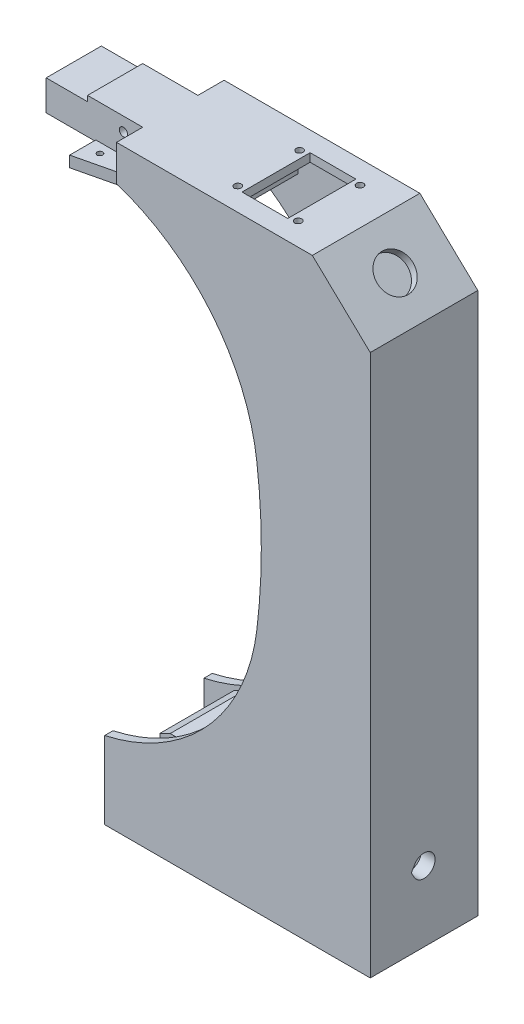
SolidWorks part; units mm, degrees
ref_plane "Спереди" through (0, 0, 0) normal (0, 0, 1) x (1, 0, 0)
ref_plane "Сверху" through (0, 0, 0) normal (0, 1, 0) x (1, 0, 0)
ref_plane "Справа" through (0, 0, 0) normal (1, 0, 0) x (0, 0, -1)
other "Configuration Table"
sketch "Эскиз1" plane through (0, 0, 0) normal (0, 0, 1) x (1, 0, 0)
  line L1 (4.2996, 175.4028) -> (4.2996, 188.4028)
  line L4 (96.2996, 0) -> (96.2996, 168.4028)
  line L7 (75.2996, 188.4028) -> (4.2996, 188.4028)
  line L11 (0, 0) -> (0, -28)
  line L12 (96.2996, 0) -> (96.2996, -28)
  line L13 (96.2996, -28) -> (0, -28)
  line L14 (75.2996, 188.4028) -> (96.2996, 168.4028)
  arc A0 (0, 0) -> (55.1731, 60.6624) centre (-15.2954, 69.3329) ccw
  arc A1 (55.1731, 113.6624) -> (4.2996, 175.4028) centre (-18.7693, 104.5645) ccw
  arc A2 (55.1731, 60.6624) -> (55.1731, 113.6624) centre (-160.2027, 87.1624) ccw
  dimension "D1" = 142
  dimension "D3" = 149
  dimension "D5" = 53
  dimension "D6" = 217
  dimension "D2" = 82
  dimension "D4" = 80
  dimension "D7" = 125.5129
  dimension "D8" = 126.3456
  dimension "D9" = 15.2954
  dimension "D10" = 69.3329
  dimension "D11" = 160.2027
  dimension "D12" = 87.1624
  dimension "D13" = 104.5645
  dimension "D14" = 18.7693
  dimension "D15" = 4.2996
  dimension "D16" = 175.4028
  dimension "D17" = 92
  dimension "D18" = 168.4028
  dimension "D19" = 71
  dimension "D20" = 28
  dimension "D21" = 96.2996
  dimension "D22" = 28
  dimension "D23" = 20
  dimension "D24" = 216.4028
extrude "Бобышка-Вытянуть6" add sketch "Эскиз1" along normal blind 39
sketch "Эскиз5" plane through (0, 0, 0) normal (0, 0, 1) x (1, 0, 0)
  line L3 (34.0996, 175.4028) -> (4.2996, 175.4028)
  line L4 (-18.7004, 169.0219) -> (-18.7004, -25)
  line L8 (34.0996, 175.4028) -> (34.0996, 185.4028)
  line L9 (34.0996, 185.4028) -> (74.0996, 185.4028)
  line L10 (74.0996, 185.4028) -> (91.2996, 169.0219)
  line L11 (96.2996, 168.4028) -> (75.2996, 188.4028) construction
  line L12 (75.2996, 188.4028) -> (4.2996, 188.4028) construction
  line L13 (-18.7004, 169.0219) -> (4.2996, 169.0219)
  line L14 (4.2996, 169.0219) -> (4.2996, 175.4028)
  line L18 (0, -28) -> (96.2996, -28) construction
  line L20 (-18.7004, -25) -> (14, -25)
  line L21 (14, 6.5) -> (14, -25)
  line L22 (91.2996, -25) -> (30.2996, -25)
  line L25 (30.2996, -25) -> (30.2996, 6.5)
  line L27 (14, 6.5) -> (30.2996, 6.5)
  line L28 (91.2996, -25) -> (91.2996, 169.0219)
  line L29 (96.2996, -28) -> (96.2996, 168.4028) construction
  dimension "D2" = 32.7004
  dimension "D3" = 31.5
  dimension "D4" = 3
  dimension "D5" = 3
  dimension "D6" = 40
  dimension "D7" = 23
  dimension "D8" = 5
  dimension "D9" = 6.381
  dimension "D10" = 14
  dimension "D11" = 3
  dimension "D12" = 3
  dimension "D14" = 61
extrude "Вырез-Вытянуть2" cut sketch "Эскиз5" along normal blind 33 from offset 3
sketch "Эскиз7" plane through (0, 0, 0) normal (0, 0, 1) x (1, 0, 0)
  line L1 (4.2996, 188.4028) -> (-30.7004, 188.4028)
  line L2 (4.2996, 188.4028) -> (4.2996, 175.4028)
  line L3 (4.2996, 175.4028) -> (-30.7004, 175.4028)
  line L4 (-30.7004, 188.4028) -> (-30.7004, 175.4028)
  dimension "D1" = 35
extrude "Бобышка-Вытянуть7" add sketch "Эскиз7" along normal blind 20 from offset 9.5
sketch "Эскиз22" plane through (0, 188.4028, 0) normal (0, 1, 0) x (1, 0, 0)
  line L0 (10.2996, -29.5) -> (10.2996, -33.5375)
  line L1 (4.2996, -9.5) -> (-30.7004, -9.5) construction
  line L2 (-12.7004, -9.5) -> (-12.7004, 0)
  line L3 (-48.7653, 0) -> (48.7653, 0) construction
  line L4 (-12.7004, 0) -> (10.2996, -5.4625)
  line L5 (10.2996, -9.5) -> (-12.7004, -9.5)
  line L6 (4.2996, -29.5) -> (-30.7004, -29.5) construction
  line L7 (-12.7004, -29.5) -> (-12.7004, -39)
  line L8 (-12.7004, -39) -> (10.2996, -33.5375)
  line L9 (10.2996, -29.5) -> (-12.7004, -29.5)
  line L10 (10.2996, -9.5) -> (10.2996, -5.4625)
  dimension "D1" = 9.5
  dimension "D2" = 13.36
  dimension "D3" = 17
  dimension "D4" = 9.5
  dimension "D5" = 13.36
  dimension "D6" = 17
  dimension "D7" = 23
extrude "Бобышка-Вытянуть8" add sketch "Эскиз22" along normal blind 4 from offset 16.5 offset against normal yes
sketch "Эскиз12" plane through (0, 0, 0) normal (0, 1, 0) x (1, 0, 0)
  line L1 (-7.7004, -34.1547) -> (-7.2004, -33.866)
  line L2 (-7.7004, -34.1547) -> (-8.2004, -33.866)
  line L4 (-7.7004, -7.1547) -> (-7.2004, -6.866)
  line L5 (-7.7004, -7.1547) -> (-8.2004, -6.866)
  arc A0 (-7.2004, -6.866) -> (-8.2004, -6.866) centre (-7.7004, -6) ccw
  arc A1 (-7.2004, -33.866) -> (-8.2004, -33.866) centre (-7.7004, -33) ccw
  dimension "D1" = 2
  dimension "D2" = 2
  dimension "D3" = 27
  dimension "D4" = 6
  dimension "D5" = 23
  dimension "D6" = 23
  dimension "D7" = 120
  dimension "D8" = 120
  dimension "D9" = 0.5
  dimension "D10" = 0.5
extrude "Вырез-Вытянуть3" cut sketch "Эскиз12" against normal blind 10 from offset 180
sketch "Эскиз13" plane through (0, 0, 0) normal (0, 0, 1) x (1, 0, 0)
  line L0 (4.2996, 188.4028) -> (-30.7004, 188.4028) construction
  line L1 (-30.7004, 188.4028) -> (-30.7004, 175.4028) construction
  circle A0 centre (-2.7004, 183.4028) radius 1.5
  dimension "D1" = 5
  dimension "D3" = 3
  dimension "D2" = 28
extrude "Вырез-Вытянуть4" cut sketch "Эскиз13" along normal blind 30
sketch "Эскиз14" plane through (0, 0, 0) normal (0, 0, 1) x (1, 0, 0)
  line L1 (-30.7004, 188.4028) -> (-15.7004, 188.4028)
  line L2 (-30.7004, 188.4028) -> (-30.7004, 186.4028)
  line L3 (-30.7004, 186.4028) -> (-15.7004, 186.4028)
  line L4 (-15.7004, 188.4028) -> (-15.7004, 186.4028)
  dimension "D1" = 2
  dimension "D2" = 15
extrude "Вырез-Вытянуть5" cut sketch "Эскиз14" along normal blind 30
sketch "Эскиз17" plane through (0, 0, 0) normal (1, 0, 0) x (0, 0, -1)
  line L1 (-24.1188, -2.5) -> (-22.9641, -0.5)
  line L2 (-24.1188, -2.5) -> (-22.9641, -4.5)
  arc A0 (-22.9641, -4.5) -> (-22.9641, -0.5) centre (-19.5, -2.5) ccw
  dimension "D1" = 8
  dimension "D2" = 2.5
  dimension "D3" = 19.5
  dimension "D4" = 120
  dimension "D5" = 2
extrude "Вырез-Вытянуть7" cut sketch "Эскиз17" along normal blind 85 from offset 17
sketch "Эскиз18" plane through (0, 0, 0) normal (1, 0, 0) x (0, 0, -1)
  line L1 (-21.8094, -2.5) -> (-21.2321, -1.5)
  line L2 (-21.8094, -2.5) -> (-21.2321, -3.5)
  arc A0 (-21.2321, -3.5) -> (-21.2321, -1.5) centre (-19.5, -2.5) ccw
  dimension "D1" = 4
  dimension "D2" = 120
  dimension "D3" = 1
extrude "Вырез-Вытянуть9" cut sketch "Эскиз18" along normal blind 5 from offset 13
sketch "Эскиз20" plane through (0, 188.4028, 0) normal (0, 1, 0) x (1, 0, 0)
  line L4 (42.65, -7.15) -> (42.65, -31.85)
  line L5 (42.65, -31.85) -> (59.25, -31.85)
  line L6 (42.65, -7.15) -> (59.25, -7.15)
  line L7 (59.25, -7.15) -> (59.25, -31.85)
  line L9 (40, -32.1434) -> (40.625, -31.7825)
  line L10 (40, -32.1434) -> (39.375, -31.7825)
  line L12 (40, -9.7434) -> (40.625, -9.3825)
  line L13 (40, -9.7434) -> (39.375, -9.3825)
  line L16 (61.9, -9.7434) -> (62.525, -9.3825)
  line L17 (61.9, -9.7434) -> (61.275, -9.3825)
  line L20 (61.9, -32.1434) -> (62.525, -31.7825)
  line L21 (61.9, -32.1434) -> (61.275, -31.7825)
  arc A0 (62.525, -9.3825) -> (61.275, -9.3825) centre (61.9, -8.3) ccw
  arc A1 (62.525, -31.7825) -> (61.275, -31.7825) centre (61.9, -30.7) ccw
  arc A2 (40.625, -9.3825) -> (39.375, -9.3825) centre (40, -8.3) ccw
  arc A3 (40.625, -31.7825) -> (39.375, -31.7825) centre (40, -30.7) ccw
  dimension "D1" = 21.9
  dimension "D13" = 2.5
  dimension "D14" = 2.5
  dimension "D15" = 2.5
  dimension "D16" = 2.5
  dimension "D2" = 22.4
  dimension "D3" = 16.6
  dimension "D4" = 24.7
  dimension "D5" = 40
  dimension "D6" = 21.9
  dimension "D7" = 22.4
  dimension "D8" = 31.3268
  dimension "D9" = 42.65
  dimension "D10" = 7.15
  dimension "D11" = 61.9
  dimension "D12" = 30.7
  dimension "D17" = 59.25
  dimension "D18" = 120
  dimension "D19" = 120
  dimension "D20" = 120
  dimension "D21" = 120
  dimension "D22" = 0.625
  dimension "D23" = 0.625
  dimension "D24" = 0.625
  dimension "D25" = 0.625
extrude "Вырез-Вытянуть10" cut sketch "Эскиз20" against normal blind 5
sketch "Эскиз21" plane through (129.9037, 136.3989, 0) normal (0.6897, 0.7241, 0) x (0, 0, -1)
  line L0 (0, 46.4057) -> (0, 75.4057) construction
  line L1 (0, 60.9057) -> (-39, 60.9057)
  line L2 (-39, 46.4057) -> (-39, 75.4057) construction
  line L3 (-19.5, 75.4057) -> (-19.5, 46.4057)
  line L4 (-39, 75.4057) -> (0, 75.4057) construction
  line L5 (-39, 46.4057) -> (0, 46.4057) construction
  circle A0 centre (-19.5, 60.9057) radius 6.5
  point P17 (-19.5, 60.9057)
  dimension "D1" = 13
extrude "Вырез-Вытянуть11" cut sketch "Эскиз21" against normal blind 5 contours A0
sketch "Эскиз23" plane through (14, 0, 0) normal (-1, 0, 0) x (0, 0, 1)
  line L0 (39, -28) -> (0, -28) construction
  line L1 (0, 0) -> (0, -28) construction
  line L5 (22.9641, -17) -> (22.0981, -15.5)
  line L6 (22.9641, -17) -> (22.0981, -18.5)
  arc A0 (22.0981, -15.5) -> (22.0981, -18.5) centre (19.5, -17) ccw
  dimension "D1" = 6
  dimension "D2" = 11
  dimension "D3" = 19.5
  dimension "D4" = 120
  dimension "D5" = 1.5
extrude "Вырез-Вытянуть12" cut sketch "Эскиз23" against normal blind 17
sketch "Эскиз24" plane through (0, 0, 3) normal (0, 0, 1) x (1, 0, 0)
  line L0 (11, -1) -> (27.1699, 6.9078)
  line L1 (27.1699, 6.9078) -> (23.6554, 14.0944)
  line L2 (23.6554, 14.0944) -> (7.4854, 6.1866)
  line L3 (7.4854, 6.1866) -> (11, -1)
  line L5 (0, -25) -> (0, 0) construction
  dimension "D1" = 18
  dimension "D2" = 8
  dimension "D3" = 27
  dimension "D4" = 11
  dimension "D5" = 26.061
extrude "Вырез-Вытянуть13" cut sketch "Эскиз24" along normal blind 3
sketch "Эскиз25" plane through (0, 0, 3) normal (0, 0, 1) x (1, 0, 0)
  line L0 (11, -1) -> (27.1699, 6.9078)
  line L1 (27.1699, 6.9078) -> (23.6554, 14.0944)
  line L2 (23.6554, 14.0944) -> (7.4854, 6.1866)
  line L3 (7.4854, 6.1866) -> (11, -1)
  line L4 (0, 0) -> (0, -28) construction
  dimension "D1" = 27
  dimension "D2" = 11
  dimension "D3" = 18
  dimension "D4" = 8
  dimension "D5" = 26.061
extrude "Вырез-Вытянуть14" cut sketch "Эскиз25" along normal blind 3 from offset 30
sketch "Эскиз26" plane through (0, 175.4028, 0) normal (0, -1, 0) x (1, 0, 0)
  line L0 (0, 39) -> (0, 0) construction
  line L1 (-12.7004, 29.5) -> (0, 29.5)
  line L2 (-12.7004, 29.5) -> (-12.7004, 9.5)
  line L3 (-12.7004, 9.5) -> (0, 9.5)
  line L4 (0, 29.5) -> (0, 9.5)
  line L5 (-12.7004, 9.5) -> (10.2996, 9.5) construction
extrude "Бобышка-Вытянуть9" add sketch "Эскиз26" along normal blind 2
sketch "Эскиз27" plane through (127.8348, 134.2265, 0) normal (-0.6897, -0.7241, 0) x (0.7241, -0.6897, 0)
  line L0 (-50.4533, 3) -> (-74.2057, 3) construction
  line L1 (-50.4533, 36) -> (-67.4533, 36)
  line L2 (-50.4533, 36) -> (-50.4533, 3)
  line L3 (-50.4533, 3) -> (-67.4533, 3)
  line L4 (-67.4533, 36) -> (-67.4533, 3)
  dimension "D1" = 17
extrude "Бобышка-Вытянуть10" add sketch "Эскиз27" along normal blind 3 from offset 7
